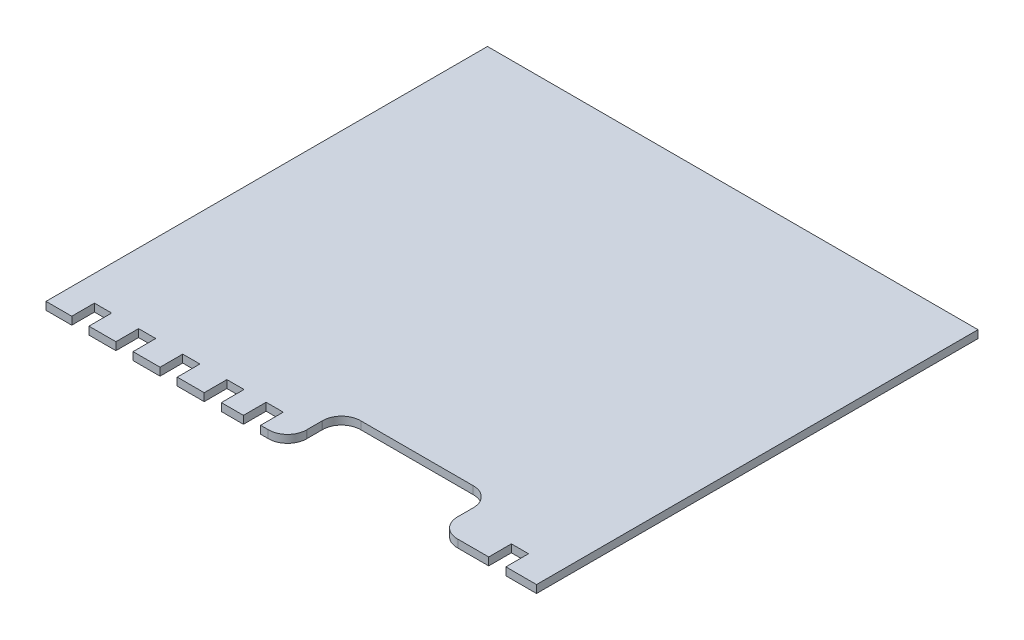
SolidWorks part; units mm, degrees
ref_plane "Front Plane" through (0, 0, 0) normal (0, 0, 1) x (1, 0, 0)
ref_plane "Top Plane" through (0, 0, 0) normal (0, 1, 0) x (1, 0, 0)
ref_plane "Right Plane" through (0, 0, 0) normal (1, 0, 0) x (0, 0, -1)
sketch "Sketch1" plane through (0, 0, 0) normal (0, 1, 0) x (1, 0, 0)
  line L13 (0, 90) -> (100, 90)
  line L14 (100, 90) -> (100, 0)
  line L15 (100, 0) -> (93.75, 0)
  line L16 (93.75, 0) -> (93.75, 4.625)
  line L17 (93.75, 4.625) -> (90.25, 4.625)
  line L18 (90.25, 4.625) -> (90.25, 0)
  line L19 (90.25, 0) -> (84, 0)
  line L20 (79.998, 3.875) -> (80, 4)
  line L21 (80, 4) -> (80, 7)
  line L22 (80, 7) -> (80.002, 7.125)
  line L23 (76, 11) -> (53.25, 11)
  line L24 (49.248, 7.125) -> (49.25, 7)
  line L25 (49.25, 7) -> (49.25, 4)
  line L26 (49.25, 4) -> (49.252, 3.875)
  line L27 (45.25, 0) -> (43.75, 0)
  line L28 (43.75, 0) -> (43.75, 4.625)
  line L29 (43.75, 4.625) -> (40.25, 4.625)
  line L30 (40.25, 4.625) -> (40.25, 0)
  line L31 (40.25, 0) -> (35.75, 0)
  line L32 (35.75, 0) -> (35.75, 4.625)
  line L33 (35.75, 4.625) -> (32.25, 4.625)
  line L34 (32.25, 4.625) -> (32.25, 0)
  line L35 (32.25, 0) -> (26.75, 0)
  line L36 (26.75, 0) -> (26.75, 4.625)
  line L37 (26.75, 4.625) -> (23.25, 4.625)
  line L38 (23.25, 4.625) -> (23.25, 0)
  line L39 (23.25, 0) -> (17.75, 0)
  line L40 (17.75, 0) -> (17.75, 4.625)
  line L41 (17.75, 4.625) -> (14.25, 4.625)
  line L42 (14.25, 4.625) -> (14.25, 0)
  line L43 (14.25, 0) -> (8.75, 0)
  line L44 (8.75, 0) -> (8.75, 4.625)
  line L45 (8.75, 4.625) -> (5.25, 4.625)
  line L46 (5.25, 4.625) -> (5.25, 0)
  line L47 (5.25, 0) -> (0, 0)
  line L48 (0, 0) -> (0, 90)
  arc A14 (79.998, 3.875) -> (84, 0) centre (83.875, 3.875) ccw
  arc A23 (80.002, 7.125) -> (76, 11) centre (76.125, 7.125) ccw
  arc A28 (53.25, 11) -> (49.248, 7.125) centre (53.125, 7.125) ccw
  arc A37 (45.25, 0) -> (49.252, 3.875) centre (45.375, 3.875) ccw
extrude "Boss-Extrude1" add sketch "Sketch1" along normal blind 1.5875
ref_plane "center-of-slot" through (0, 0.7937, 0) normal (0, 1, 0) x (1, 0, 0)
